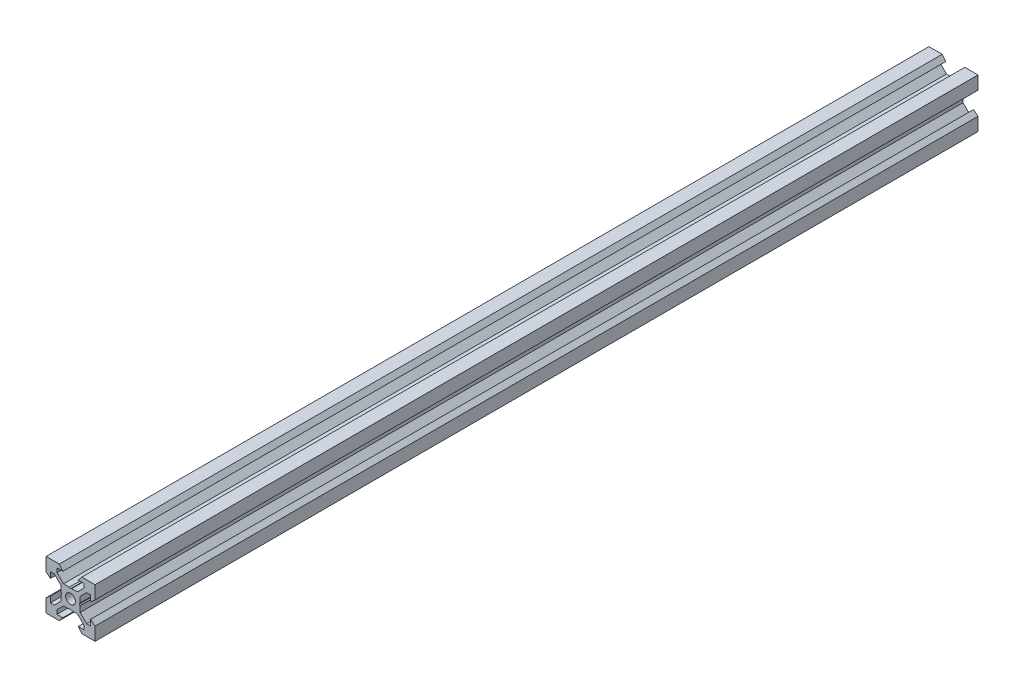
SolidWorks part; units mm, degrees
ref_plane "Front Plane" through (0, 0, 0) normal (0, 0, 1) x (1, 0, 0)
ref_plane "Top Plane" through (0, 0, 0) normal (0, 1, 0) x (1, 0, 0)
ref_plane "Right Plane" through (0, 0, 0) normal (1, 0, 0) x (0, 0, -1)
sketch "Sketch1" plane through (0, 0, 0) normal (0, 0, 1) x (1, 0, 0)
  line L0 (10, 10) -> (4.6104, 10) construction
  line L1 (10, 10) -> (10, 4.6104) construction
  line L2 (10, -10) -> (10, -4.6104) construction
  line L3 (10, -10) -> (4.6104, -10) construction
  line L4 (10, 10) -> (10, 4.6104)
  line L5 (6.5607, 5.5) -> (8.2, 5.5)
  line L6 (5.5, 8.2) -> (5.5, 6.5607)
  line L7 (10, 10) -> (4.6104, 10)
  line L8 (10, 10) -> (10, 4.6104)
  line L9 (6.5607, 5.5) -> (3.9, 2.8393)
  line L10 (5.5, 6.5607) -> (2.8393, 3.9)
  line L11 (10, 4.6104) -> (8.2, 3.1)
  line L12 (4.6104, 10) -> (3.1, 8.2)
  line L13 (8.2, 3.1) -> (8.2, 5.5)
  line L14 (3.1, 8.2) -> (5.5, 8.2)
  line L15 (-6.5607, 5.5) -> (-8.2, 5.5)
  line L16 (6.5607, -5.5) -> (8.2, -5.5)
  line L17 (3.1, -8.2) -> (5.5, -8.2)
  line L18 (8.2, -3.1) -> (8.2, -5.5)
  line L19 (4.6104, -10) -> (3.1, -8.2)
  line L20 (10, -4.6104) -> (8.2, -3.1)
  line L21 (0.5196, -3.9) -> (0, -3.6)
  line L22 (0.5196, 3.9) -> (0, 3.6)
  line L23 (3.6, 0) -> (3.9, -0.5196)
  line L24 (3.9, 0.5196) -> (3.6, 0)
  line L25 (3.9, 0.5196) -> (3.9, 2.8393)
  line L26 (2.8393, 3.9) -> (0.5196, 3.9)
  line L27 (3.9, -2.8393) -> (3.9, -0.5196)
  line L28 (2.8393, -3.9) -> (0.5196, -3.9)
  line L29 (5.5, -6.5607) -> (2.8393, -3.9)
  line L30 (6.5607, -5.5) -> (3.9, -2.8393)
  line L31 (10, -10) -> (10, -4.6104)
  line L32 (10, -10) -> (4.6104, -10)
  line L33 (5.5, -8.2) -> (5.5, -6.5607)
  line L34 (-6.5607, -5.5) -> (-8.2, -5.5)
  line L35 (10, -10) -> (10, -4.6104)
  line L36 (0, 0) -> (0, 8.2) construction
  line L37 (-10, -10) -> (-4.6104, -10) construction
  line L38 (-10, -10) -> (-10, -4.6104) construction
  line L39 (-10, 10) -> (-10, 4.6104) construction
  line L40 (-10, 10) -> (-4.6104, 10) construction
  line L41 (-10, -10) -> (-10, -4.6104)
  line L43 (-5.5, -8.2) -> (-5.5, -6.5607)
  line L44 (-10, -10) -> (-4.6104, -10)
  line L45 (-10, -10) -> (-10, -4.6104)
  line L46 (-6.5607, -5.5) -> (-3.9, -2.8393)
  line L47 (-5.5, -6.5607) -> (-2.8393, -3.9)
  line L48 (-2.8393, -3.9) -> (-0.5196, -3.9)
  line L49 (-3.9, -2.8393) -> (-3.9, -0.5196)
  line L50 (-2.8393, 3.9) -> (-0.5196, 3.9)
  line L51 (-3.9, 0.5196) -> (-3.9, 2.8393)
  line L52 (-3.9, 0.5196) -> (-3.6, 0)
  line L53 (-3.6, 0) -> (-3.9, -0.5196)
  line L54 (-0.5196, 3.9) -> (0, 3.6)
  line L55 (-0.5196, -3.9) -> (0, -3.6)
  line L56 (-10, -4.6104) -> (-8.2, -3.1)
  line L57 (-4.6104, -10) -> (-3.1, -8.2)
  line L58 (-8.2, -3.1) -> (-8.2, -5.5)
  line L59 (-3.1, -8.2) -> (-5.5, -8.2)
  line L60 (-10, -10) -> (10, -10) construction
  line L61 (-10, -10) -> (-10, 10) construction
  line L62 (-3.1, 8.2) -> (-5.5, 8.2)
  line L63 (-8.2, 3.1) -> (-8.2, 5.5)
  line L64 (-4.6104, 10) -> (-3.1, 8.2)
  line L65 (-10, 4.6104) -> (-8.2, 3.1)
  line L66 (-5.5, 6.5607) -> (-2.8393, 3.9)
  line L67 (-6.5607, 5.5) -> (-3.9, 2.8393)
  line L68 (-10, 10) -> (-10, 4.6104)
  line L69 (-10, 10) -> (-4.6104, 10)
  line L70 (-5.5, 8.2) -> (-5.5, 6.5607)
  line L71 (-10, 10) -> (10, 10) construction
  line L72 (-10, 10) -> (-10, 4.6104)
  line L73 (10, -10) -> (10, 10) construction
  line L74 (-10, -10) -> (10, 10) construction
  line L75 (-10, 10) -> (10, -10) construction
  circle A0 centre (0, 0) radius 2
  dimension "D7" = 4
  dimension "D1" = 20
  dimension "D2" = 5.3896
  dimension "D3" = 4.5
  dimension "D4" = 50
  dimension "D5" = 1.8
  dimension "D6" = 1.5104
  dimension "D8" = 5.5
  dimension "D9" = 120
  dimension "D10" = 0.3
  dimension "D11" = 2.3197
  dimension "D12" = 7.8
  dimension "D13" = 7.8
  dimension "D14" = 1.5
  dimension "D15" = 2.6607
extrude "Boss-Extrude1" add sketch "Sketch1" along normal mid plane 360 contours L70 L62 L64 L69 L68 L65 L63 L15 L67 L51 L52 L53 L49 L46 L34 L58 L56 L41 L44 L57 L59 L43 L47 L48 L55 L21 L28 L29 L33 L17 L19 L32 L31 L20 L18 L16 L30 L27 L23 L24 L25 L9 L5 L13 L11 L4 L7 L12 L14 L6 L10
